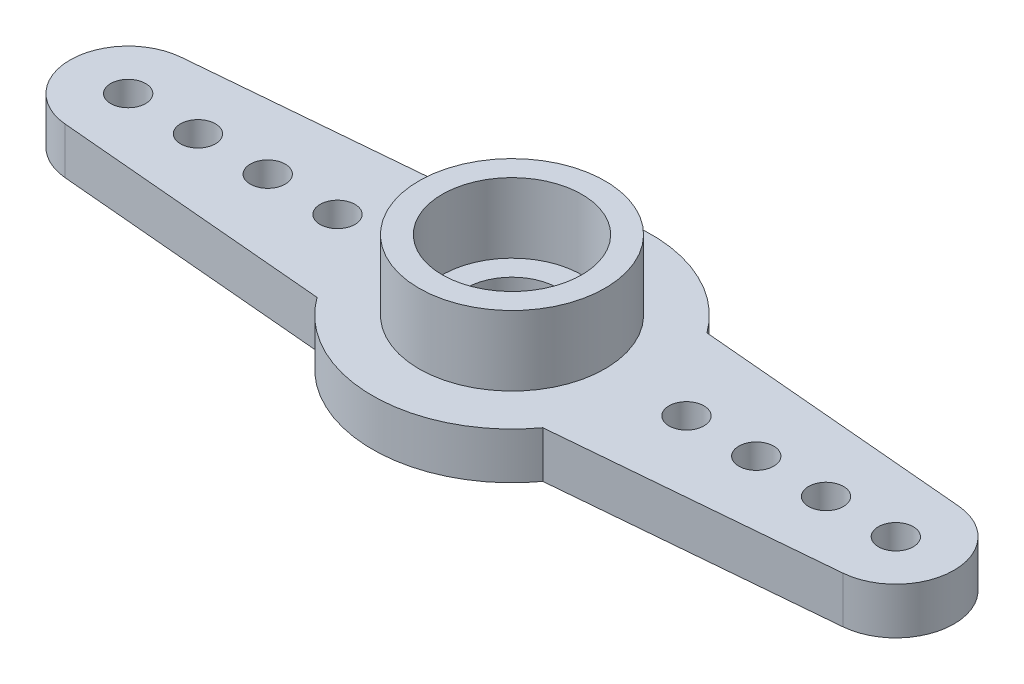
SolidWorks part; units mm, degrees
ref_plane "Front Plane" through (0, 0, 0) normal (0, 0, 1) x (1, 0, 0)
ref_plane "Top Plane" through (0, 0, 0) normal (0, 1, 0) x (1, 0, 0)
ref_plane "Right Plane" through (0, 0, 0) normal (1, 0, 0) x (0, 0, -1)
sketch "Sketch1" plane through (0, 0, 0) normal (0, 1, 0) x (1, 0, 0)
  line L0 (-19, 0) -> (19, 0) construction
  line L1 (16.7179, -2.4905) -> (4.8528, -3.5286)
  line L2 (16.7179, 2.4905) -> (4.8528, 3.5286)
  line L3 (0, -6.6) -> (0, 6.6) construction
  line L4 (-16.7179, 2.4905) -> (-4.8528, 3.5286)
  line L5 (-16.7179, -2.4905) -> (-4.8528, -3.5286)
  circle A0 centre (0, 0) radius 2
  circle A1 centre (7.5, 0) radius 0.75
  circle A2 centre (10.5, 0) radius 0.75
  circle A3 centre (13.5, 0) radius 0.75
  circle A4 centre (16.5, 0) radius 0.75
  arc A5 (4.8528, 3.5286) -> (-4.8528, 3.5286) centre (0, 0) ccw
  arc A6 (16.7179, -2.4905) -> (16.7179, 2.4905) centre (16.5, 0) ccw
  arc A7 (-16.7179, -2.4905) -> (-16.7179, 2.4905) centre (-16.5, 0) cw
  circle A8 centre (-16.5, 0) radius 0.75
  circle A9 centre (-13.5, 0) radius 0.75
  circle A10 centre (-10.5, 0) radius 0.75
  circle A11 centre (-7.5, 0) radius 0.75
  arc A12 (-4.8528, -3.5286) -> (4.8528, -3.5286) centre (0, 0) ccw
  point P4 (0, 0)
  dimension "D1" = 4
  dimension "D2" = 7.5
  dimension "D3" = 1.5
  dimension "D4" = 1.5
  dimension "D6" = 1.5
  dimension "D7" = 1.5
  dimension "D11" = 12
  dimension "D12" = 2.5
  dimension "D5" = 3
  dimension "D8" = 3
  dimension "D9" = 3
  dimension "D10" = 38
  dimension "D13" = 5
  dimension "D14" = 5
extrude "Boss-Extrude1" add sketch "Sketch1" along normal blind 2
sketch "Sketch2" plane through (0, 2, 0) normal (0, 1, 0) x (1, 0, 0)
  circle A0 centre (0, 0) radius 4
  circle A1 centre (0, 0) radius 3
  dimension "D1" = 8
  dimension "D2" = 1
extrude "Boss-Extrude2" add sketch "Sketch2" along normal blind 3
